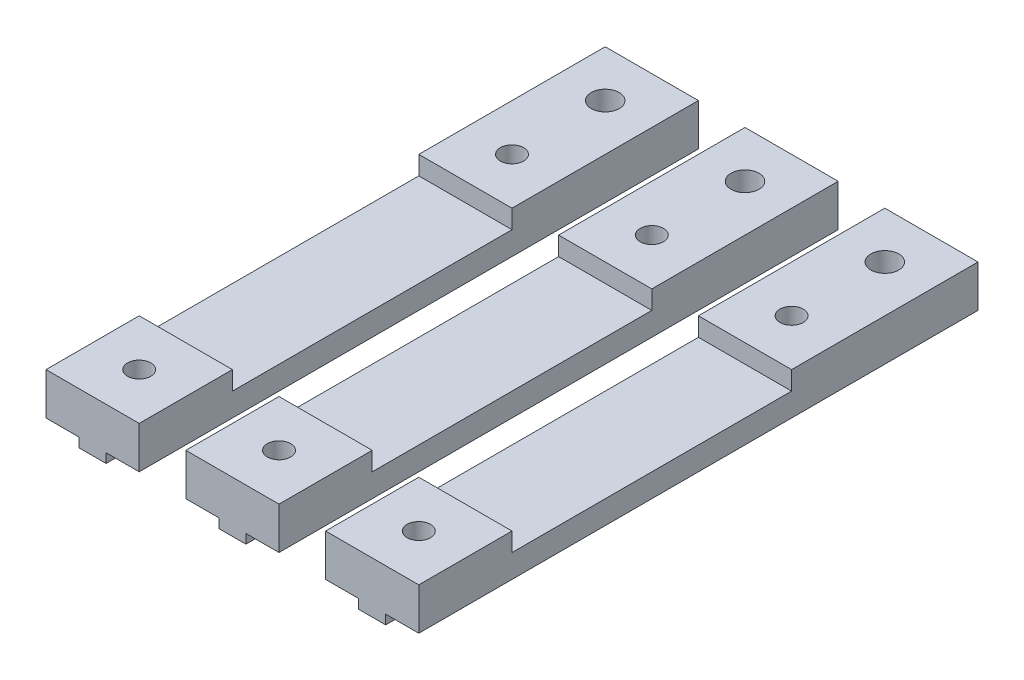
SolidWorks part; units mm, degrees
ref_plane "Front Plane" through (0, 0, 0) normal (0, 0, 1) x (1, 0, 0)
ref_plane "Top Plane" through (0, 0, 0) normal (0, 1, 0) x (1, 0, 0)
ref_plane "Right Plane" through (0, 0, 0) normal (1, 0, 0) x (0, 0, -1)
sketch "Sketch1" plane through (0, 0, 0) normal (0, 0, 1) x (1, 0, 0)
  line L0 (-5, 0) -> (5, 0)
  line L1 (5, 0) -> (5, -4.5)
  line L2 (5, -4.5) -> (1.45, -4.5)
  line L3 (1.45, -4.5) -> (1.45, -5.5)
  line L4 (1.45, -5.5) -> (-1.45, -5.5)
  line L5 (-1.45, -5.5) -> (-1.45, -4.5)
  line L6 (-1.45, -4.5) -> (-5, -4.5)
  line L7 (-5, -4.5) -> (-5, 0)
  point P9 (0, 0)
  dimension "D1" = 10
  dimension "D2" = 4.5
  dimension "D3" = 1
  dimension "D4" = 2.9
extrude "Main" add sketch "Sketch1" along normal blind 60
sketch "Sketch2" plane through (0, 0, 0) normal (0, 1, 0) x (1, 0, 0)
  line L0 (5, -60) -> (-5, -60) construction
  line L1 (5, 0) -> (-5, 0) construction
  circle A0 centre (0, -55) radius 1.25
  circle A1 centre (0, -15) radius 1.25
  circle A2 centre (0, -5) radius 1.5
  dimension "D1" = 2.5
  dimension "D4" = 3
  dimension "D2" = 5
  dimension "D3" = 40
  dimension "D5" = 5
extrude "I2CBoardFixHole" cut sketch "Sketch2" against normal through all
sketch "Sketch3" plane through (0, 0, 0) normal (0, 1, 0) x (1, 0, 0)
  line L1 (-5, -60) -> (-5, 0) construction
  line L5 (5, -60) -> (5, 0) construction
  line L6 (-5, -20) -> (5, -20)
  line L7 (-5, -20) -> (-5, -50)
  line L8 (-5, -50) -> (5, -50)
  line L9 (5, -20) -> (5, -50)
  line L10 (5, -60) -> (-5, -60) construction
  dimension "D2" = 30
  dimension "D3" = 10
extrude "Pins" cut sketch "Sketch3" against normal blind 2
pattern_linear "LPattern1" count 3 spacing 15 along (-1, 0, 0) of bodies 103
